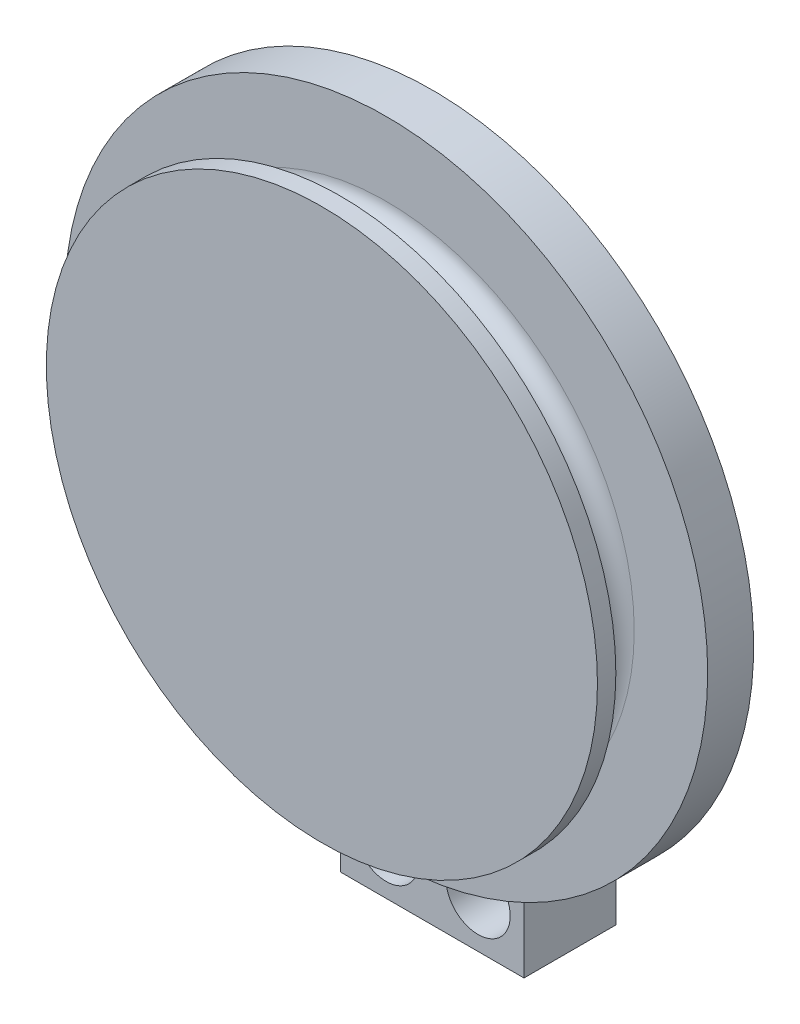
SolidWorks part; units mm, degrees
ref_plane "Front Plane" through (0, 0, 0) normal (0, 0, 1) x (1, 0, 0)
ref_plane "Top Plane" through (0, 0, 0) normal (0, 1, 0) x (1, 0, 0)
ref_plane "Right Plane" through (0, 0, 0) normal (1, 0, 0) x (0, 0, -1)
sketch "Sketch1" plane through (0, 0, 0) normal (0, 0, 1) x (1, 0, 0)
  circle A0 centre (0, 0) radius 4.1
  dimension "D1" = 8.2
extrude "Boss-Extrude1" add sketch "Sketch1" along normal blind 7
sketch "Sketch2" plane through (0, 0, 7) normal (0, 0, 1) x (1, 0, 0)
  circle A0 centre (0, 0) radius 6.25
  dimension "D1" = 12.5
extrude "Boss-Extrude2" add sketch "Sketch2" along normal blind 2
sketch "Sketch3" plane through (0, 0, 9) normal (0, 0, 1) x (1, 0, 0)
  circle A0 centre (0, 0) radius 35
  dimension "D1" = 70
extrude "Boss-Extrude3" add sketch "Sketch3" along normal blind 5
sketch "Sketch4" plane through (0, 0, 14) normal (0, 0, 1) x (1, 0, 0)
  circle A0 centre (0, 0) radius 25
  dimension "D1" = 50
extrude "Boss-Extrude4" add sketch "Sketch4" along normal blind 5
sketch "Sketch5" plane through (0, 0, 19) normal (0, 0, 1) x (1, 0, 0)
  circle A0 centre (0, 0) radius 30
extrude "Boss-Extrude5" add sketch "Sketch5" along normal blind 2
fillet "Fillet1" radius 2 1 edges at (25, 0, 19)
fillet "Fillet2" radius 2 1 edges at (25, 0, 14)
sketch "Sketch6" plane through (0, 0, 0) normal (0, 1, 0) x (1, 0, 0)
  line L0 (0, 0) -> (0, -39.6093) construction
  line L1 (25, -16) -> (-25, -16) construction
  line L2 (0, -16) -> (-30.3763, -16) construction
  line L3 (2.9572, -17) -> (-29.7434, -17) construction
  line L4 (25, -17) -> (-25, -17) construction
  line L5 (0.5721, -17) -> (-0.5375, -17) construction
  line L6 (0.0173, -17) -> (0, -16) construction
  circle A0 centre (0.0086, -16.5) radius 1.5
  dimension "D1" = 3
extrude "Cut-Extrude1" cut sketch "Sketch6" against normal through all both and the other way through all contours A0
sketch "Sketch7" plane through (0, 0, 9) normal (0, 0, -1) x (-1, 0, 0)
  line L0 (35, 0) -> (27, 0)
  line L1 (10, -33.541) -> (10, -33.7353)
  line L2 (10, -33.541) -> (10, -66.6674) construction
  line L3 (10, -33.7353) -> (10, -43.7353)
  line L7 (-10, -25.0799) -> (-10, -43.7353)
  line L8 (-10, -43.7353) -> (10, -43.7353)
  arc A0 (-10, -25.0799) -> (27, 0) centre (0, 0) ccw
  arc A2 (10, -33.541) -> (35, 0) centre (0, 0) ccw
  dimension "D3" = 10
extrude "Boss-Extrude6" add sketch "Sketch7" along normal blind 10
sketch "Sketch9" plane through (0, 0, -1) normal (0, 0, -1) x (-1, 0, 0)
  line L3 (0, -38.6855) -> (-0.0938, -38.6382)
  line L4 (10, -33.541) -> (0, -43.7353) construction
  line L5 (0, -38.6382) -> (-0.0938, -38.6382)
  line L8 (0, -43.7353) -> (0, -35) construction
  line L9 (-10, -43.7353) -> (10, -43.7353) construction
  line L10 (0, -43.7353) -> (-10, -33.541) construction
  circle A1 centre (0, 0) radius 35 construction
  circle A2 centre (5, -38.6382) radius 1.75
  circle A3 centre (-5, -38.6382) radius 1.75
  dimension "D1" = 3.5
extrude "Cut-Extrude2" cut sketch "Sketch9" against normal through all both and the other way through all contours A2 | A3
sketch "Sketch10" plane through (0, 0, 9) normal (0, 0, 1) x (1, 0, 0)
  circle A2 centre (-5, -38.6382) radius 3.5
  circle A3 centre (5, -38.6382) radius 3.5
  dimension "D1" = 7
extrude "Cut-Extrude3" cut sketch "Sketch10" against normal blind 6
